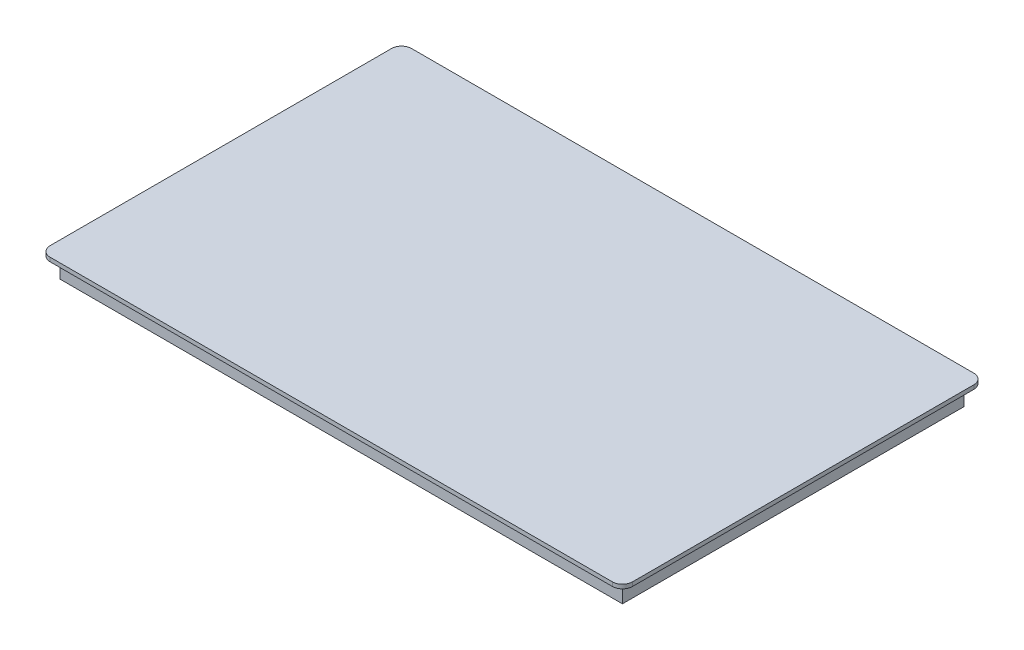
SolidWorks part; units mm, degrees
ref_plane "Front Plane" through (0, 0, 0) normal (0, 0, 1) x (1, 0, 0)
ref_plane "Top Plane" through (0, 0, 0) normal (0, 1, 0) x (1, 0, 0)
ref_plane "Right Plane" through (0, 0, 0) normal (1, 0, 0) x (0, 0, -1)
sketch "Sketch1" plane through (0, 0, 0) normal (0, 1, 0) x (1, 0, 0)
  line L1 (-72.5, 45) -> (72.5, 45)
  line L2 (-72.5, 45) -> (-72.5, -45)
  line L3 (-72.5, -45) -> (72.5, -45)
  line L4 (72.5, 45) -> (72.5, -45)
  line L5 (-72.5, 45) -> (72.5, -45) construction
  line L6 (-72.5, -45) -> (72.5, 45) construction
  point P0 (0, 0)
  dimension "D1" = 90
  dimension "D2" = 145
extrude "Boss-Extrude1" add sketch "Sketch1" against normal blind 1
sketch "Sketch2" plane through (0, -1, 0) normal (0, -1, 0) x (1, 0, 0)
  line L0 (-67.5, 40) -> (67.5, 40)
  line L1 (-70, 42.5) -> (70, 42.5)
  line L2 (-70, 42.5) -> (-70, -42.5)
  line L3 (-70, -42.5) -> (70, -42.5)
  line L4 (70, 42.5) -> (70, -42.5)
  line L5 (-70, 42.5) -> (70, -42.5) construction
  line L6 (-70, -42.5) -> (70, 42.5) construction
  line L7 (67.5, 40) -> (67.5, -40)
  line L8 (-67.5, -40) -> (67.5, -40)
  line L9 (-67.5, 40) -> (-67.5, -40)
  point P0 (0, 0)
  dimension "D1" = 140
  dimension "D2" = 85
  dimension "D3" = 2.5
extrude "Boss-Extrude2" add sketch "Sketch2" along normal blind 5
fillet "Fillet1" radius 2.5 4 edges at (72.5, -0.5, -45) (72.5, -0.5, 45) (-72.5, -0.5, -45) (-72.5, -0.5, 45)
